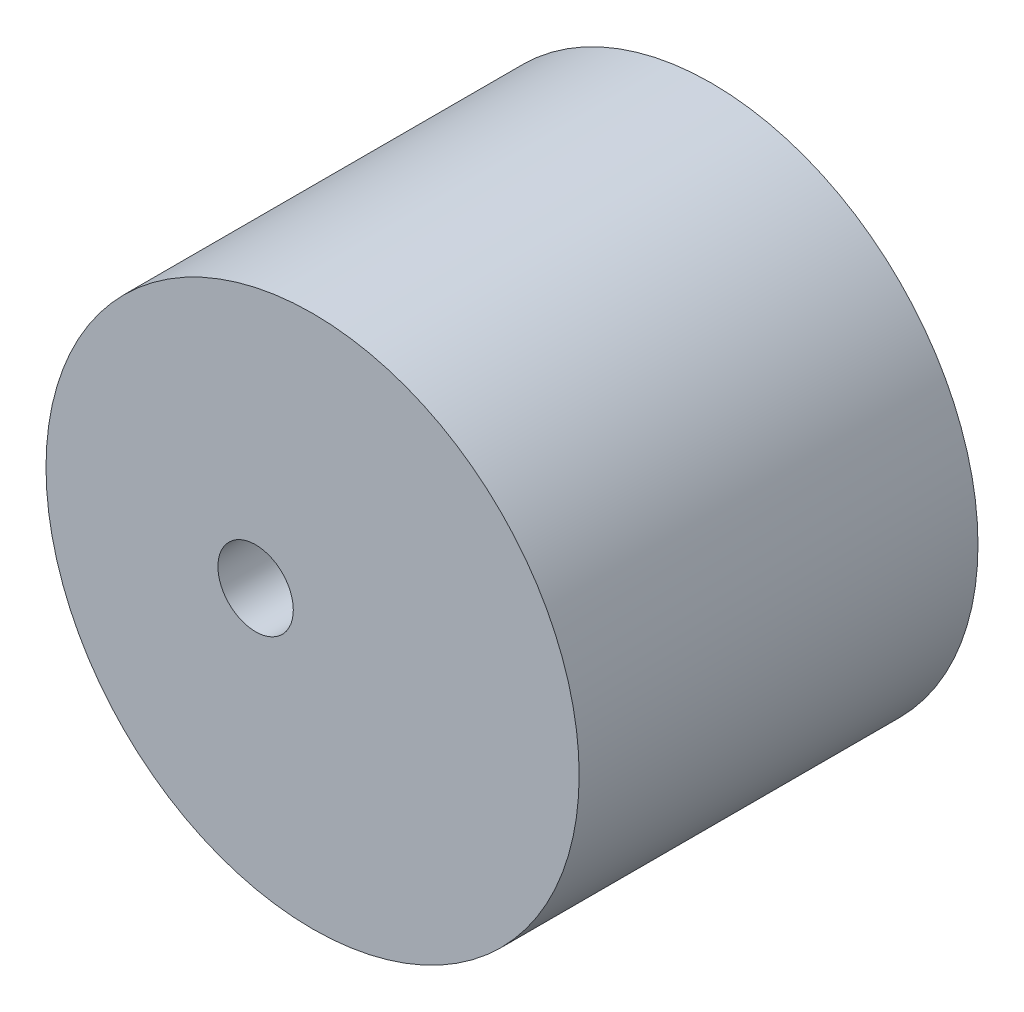
SolidWorks part; units mm, degrees
ref_plane "Front Plane" through (0, 0, 0) normal (0, 0, 1) x (1, 0, 0)
ref_plane "Top Plane" through (0, 0, 0) normal (0, 1, 0) x (1, 0, 0)
ref_plane "Right Plane" through (0, 0, 0) normal (1, 0, 0) x (0, 0, -1)
sketch "Sketch11" plane through (0, 0, 0) normal (0, 0, 1) x (1, 0, 0)
  circle A0 centre (0, 0) radius 23.3938
  circle A1 centre (-5, 0) radius 3.3085
  point P4 (0, 0)
  point P5 (0, 0)
  point P6 (0, 0)
extrude "Boss-Extrude13" add sketch "Sketch11" along normal blind 35
